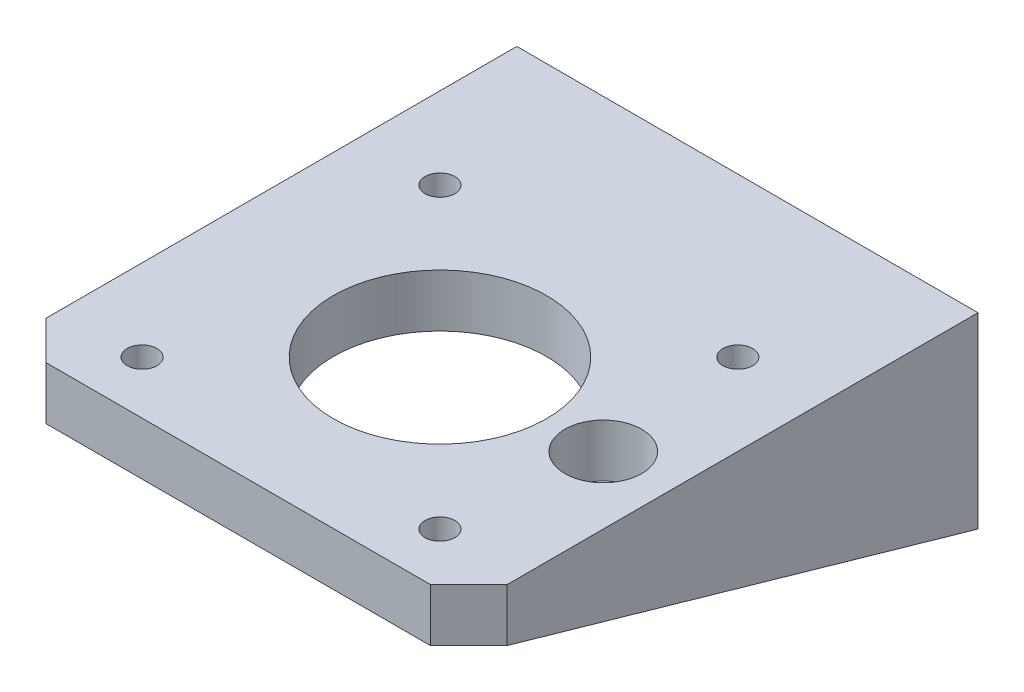
SolidWorks part; units mm, degrees
ref_plane "Alzado" through (0, 0, 0) normal (0, 0, 1) x (1, 0, 0)
ref_plane "Planta" through (0, 0, 0) normal (0, 1, 0) x (1, 0, 0)
ref_plane "Vista lateral" through (0, 0, 0) normal (1, 0, 0) x (0, 0, -1)
sketch "Croquis1" plane through (0, 0, 0) normal (0, 1, 0) x (1, 0, 0)
  line L0 (0, 4) -> (0, 49)
  line L1 (4, 53) -> (44, 53)
  line L2 (48, 49) -> (48, 4)
  line L3 (44, 0) -> (4, 0)
  line L4 (0, 49) -> (4, 53)
  line L5 (44, 53) -> (48, 49)
  line L6 (48, 4) -> (44, 0)
  line L7 (4, 0) -> (0, 4)
  circle A0 centre (8.5, 36.5) radius 1.55
  circle A1 centre (39.5, 36.5) radius 1.55
  circle A2 centre (8.5, 5.5) radius 1.55
  circle A3 centre (39.5, 5.5) radius 1.55
  circle A4 centre (24, 21) radius 11.1
  circle A5 centre (41, 21) radius 4
  point P0 (0, 0)
  point P1 (0, 53)
  point P4 (48, 53)
  point P5 (48, 0)
  dimension "D4" = 3.1
  dimension "D7" = 3.1
  dimension "D14" = 3.1
  dimension "D18" = 3.1
  dimension "D19" = 22.2
  dimension "D22" = 8
  dimension "D1" = 53
  dimension "D2" = 48
  dimension "D3" = 31
  dimension "D5" = 8.5
  dimension "D6" = 16.5
  dimension "D8" = 0
  dimension "D13" = 0
  dimension "D15" = 31
  dimension "D16" = 0
  dimension "D17" = 31
  dimension "D20" = 21
  dimension "D21" = 24
  dimension "D23" = 0
  dimension "D24" = 17
extrude "Saliente-Extruir1" add sketch "Croquis1" along normal blind 5.5
sketch "Croquis3" plane through (0, 5.5, 0) normal (0, 1, 0) x (1, 0, 0)
  line L0 (4, 53) -> (0, 53)
  line L1 (0, 53) -> (0, 49)
  line L10 (4, 53) -> (0, 49)
  line L11 (0, 49) -> (0, 4)
  line L12 (0, 4) -> (4, 0)
  line L13 (4, 0) -> (44, 0)
  line L14 (44, 0) -> (48, 4)
  line L15 (48, 4) -> (48, 49)
  line L16 (48, 49) -> (44, 53)
  line L17 (44, 53) -> (4, 53)
  line L18 (4, 53) -> (0, 49)
  dimension "D1" = 0
extrude "Saliente-Extruir2" add sketch "Croquis3" against normal blind 5.5
sketch "Croquis4" plane through (0, 0, 0) normal (-1, 0, 0) x (0, 0, 1)
  line L2 (-53, 0) -> (-53, 5.5) construction
  line L3 (-53, 0) -> (-53, 5.5)
  line L4 (-53, 0) -> (-53, -14)
  line L5 (-53, -14) -> (-4, 0)
  line L6 (-53, 5.5) -> (-4, 5.5)
  line L7 (-4, 5.5) -> (-4, 0) construction
  line L8 (-4, 5.5) -> (-4, 0)
  dimension "D1" = 14
extrude "Saliente-Extruir3" add sketch "Croquis4" against normal blind 3
sketch "Croquis5" plane through (0, 5.5, 0) normal (0, 1, 0) x (1, 0, 0)
  line L0 (48, 49) -> (48, 53)
  line L1 (48, 53) -> (44, 53)
  line L9 (0, 53) -> (0, 4)
  line L10 (0, 4) -> (4, 0)
  line L11 (4, 0) -> (44, 0)
  line L12 (44, 0) -> (48, 4)
  line L13 (48, 4) -> (48, 49)
  line L14 (48, 49) -> (44, 53)
  line L15 (44, 53) -> (0, 53)
  line L21 (48, 49) -> (44, 53)
  dimension "D1" = 0
extrude "Saliente-Extruir4" add sketch "Croquis5" against normal blind 5.5
sketch "Croquis6" plane through (48, 0, 0) normal (1, 0, 0) x (0, 0, -1)
  line L0 (4, 5.5) -> (4, 0) construction
  line L1 (53, 0) -> (53, 5.5) construction
  line L2 (4, 5.5) -> (53, 5.5) construction
  line L3 (53, 0) -> (53, -14) construction
  line L4 (53, -14) -> (4, 0) construction
  line L5 (4, 5.5) -> (4, 0)
  line L6 (53, 0) -> (53, 5.5)
  line L7 (4, 5.5) -> (53, 5.5)
  line L8 (53, 0) -> (53, -14)
  line L9 (53, -14) -> (4, 0)
extrude "Saliente-Extruir5" add sketch "Croquis6" against normal blind 3
sketch "Croquis7" plane through (0, 0, 0) normal (0, -1, 0) x (1, 0, 0)
  line L0 (45, -53) -> (3, -53)
  line L1 (3, -53) -> (3, -44)
  line L2 (3, -4) -> (3, -53) construction
  line L3 (3, -44) -> (45, -44)
  line L4 (45, -53) -> (45, -21) construction
  line L5 (45, -44) -> (45, -53)
  dimension "D1" = 9
extrude "Saliente-Extruir6" add sketch "Croquis7" along normal blind 14
sketch "Croquis9" plane through (0, 0, -44) normal (0, 0, 1) x (1, 0, 0)
  line L0 (3, -11.4286) -> (3, 0) construction
  line L1 (3, -11.4286) -> (3, 0)
  circle A0 centre (9, -5.7143) radius 1.55
  circle A1 centre (39, -5.7143) radius 1.55
  point P7 (3, -5.7143)
  dimension "D1" = 3.1
  dimension "D2" = 3.1
  dimension "D3" = 0
  dimension "D4" = 30
  dimension "D5" = 0
  dimension "D6" = 6
extrude "Cortar-Extruir1" cut sketch "Croquis9" against normal up to surface (9 mm away) contours A0 | A1 up to face at (24, -7.5, -53)
sketch "Croquis10" plane through (0, 0, -44) normal (0, 0, 1) x (1, 0, 0)
  circle A0 centre (39, -5.7143) radius 1.55 construction
  circle A1 centre (9, -5.7143) radius 1.55 construction
  circle A2 centre (39, -5.7143) radius 1.55
  circle A3 centre (9, -5.7143) radius 1.55
  circle A4 centre (9, -5.7143) radius 2.85
  circle A5 centre (39, -5.7143) radius 2.85
  circle M1 centre (39, -5.7143) radius 1.55
  circle M2 centre (9, -5.7143) radius 1.55
  dimension "D1" = 5.7
  dimension "D2" = 5.7
extrude "Cortar-Extruir2" cut sketch "Croquis10" against normal blind 3 contours A4 M2 | A5 M1
sketch "Croquis11" plane through (3, 0, 0) normal (-1, 0, 0) x (0, 0, 1)
  line L3 (-44, -11.4286) -> (-53, -14)
  line L4 (-53, -14) -> (-44, -14)
  line L5 (-44, -14) -> (-44, -11.4286)
  line L6 (-44, -11.4286) -> (-53, -14)
  line L7 (-53, -14) -> (-44, -14)
  line L8 (-44, -14) -> (-44, -11.4286)
  dimension "D1" = 0
extrude "Cortar-Extruir3" cut sketch "Croquis11" against normal through all both and the other way through all
